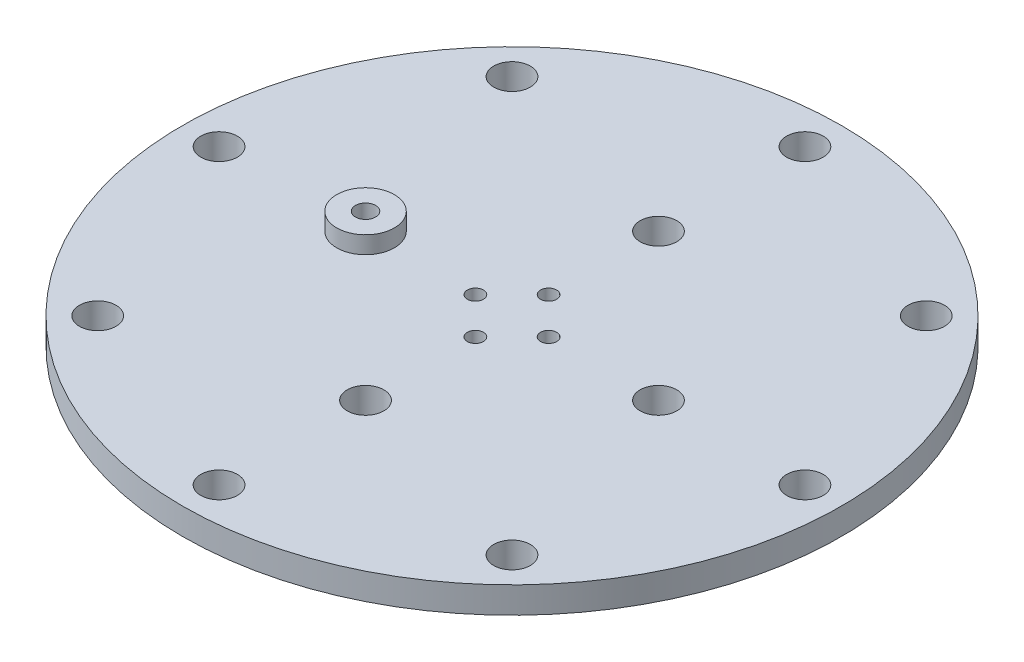
SolidWorks part; units mm, degrees
ref_plane "Front Plane" through (0, 0, 0) normal (0, 0, 1) x (1, 0, 0)
ref_plane "Top Plane" through (0, 0, 0) normal (0, 1, 0) x (1, 0, 0)
ref_plane "Right Plane" through (0, 0, 0) normal (1, 0, 0) x (0, 0, -1)
sketch "Sketch1" plane through (0, 0, 0) normal (0, 1, 0) x (1, 0, 0)
  line L0 (0, 0) -> (0, 57.15) construction
  circle A0 centre (0, 0) radius 57.15
  circle A1 centre (0, 6.35) radius 1.397
  circle A2 centre (0, 25.4) radius 3.175
  circle A3 centre (0, 50.8) radius 3.175
  circle A4 centre (25.4, 0) radius 3.175
  circle A5 centre (0, -25.4) radius 3.175
  circle A6 centre (-25.4, 0) radius 3.175
  circle A7 centre (6.35, 0) radius 1.397
  circle A8 centre (0, -6.35) radius 1.397
  circle A9 centre (-6.35, 0) radius 1.397
  circle A10 centre (35.921, 35.921) radius 3.175
  circle A11 centre (50.8, 0) radius 3.175
  circle A12 centre (35.921, -35.921) radius 3.175
  circle A13 centre (0, -50.8) radius 3.175
  circle A14 centre (-35.921, -35.921) radius 3.175
  circle A15 centre (-50.8, 0) radius 3.175
  circle A16 centre (-35.921, 35.921) radius 3.175
  point P19 (0, 0)
  point P26 (0, 0)
  point P40 (0, 0)
  dimension "D1" = 114.3
  dimension "D5" = 2.794
  dimension "D6" = 6.35
  dimension "D2" = 6.35
  dimension "D3" = 25.4
  dimension "D4" = 50.8
  dimension "D7" = 4
  dimension "D8" = 4
  dimension "D9" = 8
extrude "Boss-Extrude1" add sketch "Sketch1" along normal blind 4.572
sketch "Sketch2" plane through (0, 4.572, 0) normal (0, 1, 0) x (1, 0, 0)
  circle A0 centre (-25.4, 0) radius 2.75
  circle A1 centre (-25.4, 0) radius 1.75
  dimension "D1" = 3.5
  dimension "D2" = 5.5
extrude "Boss-Extrude2" add sketch "Sketch2" against normal blind 2 separate body
sketch "Sketch3" plane through (0, 4.572, 0) normal (0, 1, 0) x (1, 0, 0)
  circle A0 centre (-25.4, 0) radius 5
  circle A2 centre (-25.4, 0) radius 1.75 construction
  circle A3 centre (-25.4, 0) radius 1.75
  dimension "D1" = 10
extrude "Boss-Extrude3" add sketch "Sketch3" along normal blind 3
sketch "Sketch4" plane through (0, 7.572, 0) normal (0, 1, 0) x (1, 0, 0)
  line L0 (-38.1823, -7.8495) -> (-58.9053, 25.8965)
  line L1 (-33.3408, 41.5954) -> (-12.6177, 7.8495)
  line L2 (-43.662, 32.2509) -> (-36.0724, 8.1147) construction
  line L3 (-40.6332, 33.2033) -> (-33.0436, 9.0671)
  line L4 (-46.6908, 31.2985) -> (-39.1012, 7.1623)
  line L5 (-39.8672, 20.1828) -> (0, 25.4) construction
  arc A0 (-38.1823, -7.8495) -> (-12.6177, 7.8495) centre (-25.4, 0) ccw
  circle A2 centre (-25.4, 0) radius 1.75 construction
  circle A3 centre (-25.4, 0) radius 1.75
  arc A4 (-58.9053, 25.8965) -> (-33.3408, 41.5954) centre (-46.123, 33.7459) cw
  circle A9 centre (0, 0) radius 57.15 construction
  arc A10 (-40.6332, 33.2033) -> (-46.6908, 31.2985) centre (-43.662, 32.2509) ccw
  arc A11 (-39.1012, 7.1623) -> (-33.0436, 9.0671) centre (-36.0724, 8.1147) ccw
  point P14 (-39.8672, 20.1828)
  point P22 (-36.845, 22.881)
  point P23 (-43.372, 33.7459)
  point P24 (-44.1941, 33.1926)
  point P25 (-43.5586, 38.2856)
  point P26 (-45.2201, 25.8965)
  point P27 (-40.7312, 24.1283)
  point P28 (-42.5231, 32.898)
  point P29 (-42.0962, 18.2962)
  point P30 (-44.1957, 26.9787)
  point P31 (-40.345, 12.7214)
  point P32 (-40.606, 19.2495)
  point P33 (-36.7813, 9.787)
  point P34 (-33.0969, 21.0688)
  dimension "D1" = 30
  dimension "D2" = 15
  dimension "D3" = 3.175
  dimension "D4" = 80
  dimension "D5" = 40
